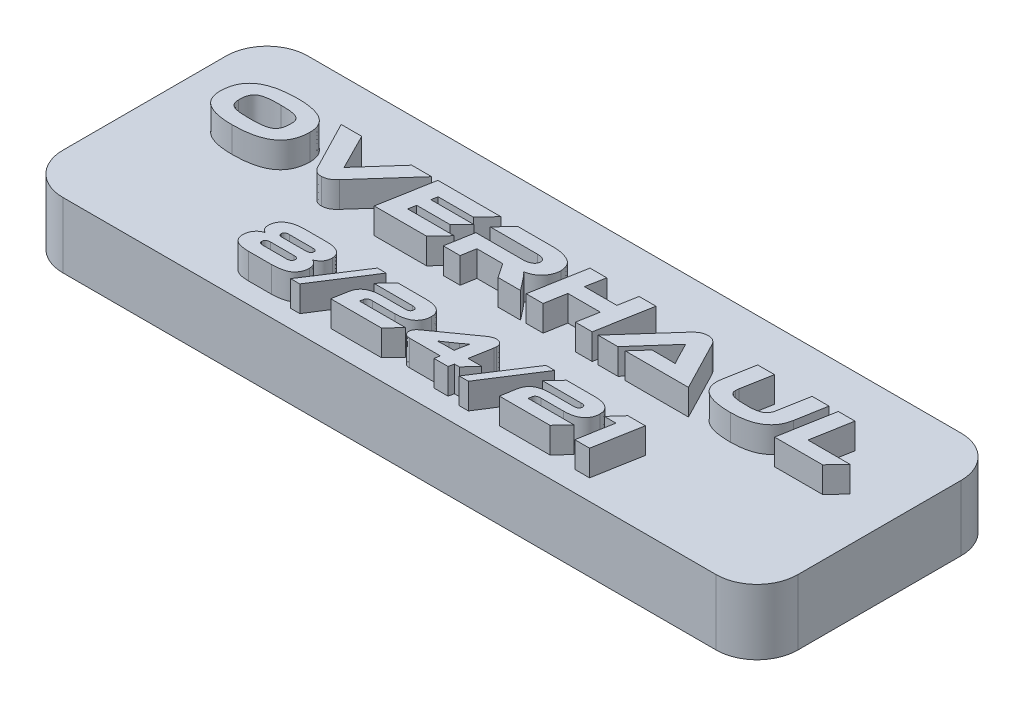
SolidWorks part; units mm, degrees
ref_plane "Front Plane" through (0, 0, 0) normal (0, 0, 1) x (1, 0, 0)
ref_plane "Top Plane" through (0, 0, 0) normal (0, 1, 0) x (1, 0, 0)
ref_plane "Right Plane" through (0, 0, 0) normal (1, 0, 0) x (0, 0, -1)
sketch "Sketch1" plane through (0, 0, 0) normal (0, 1, 0) x (1, 0, 0)
  line L1 (-28.575, 9.525) -> (28.575, 9.525)
  line L2 (-28.575, 9.525) -> (-28.575, -9.525)
  line L3 (-28.575, -9.525) -> (28.575, -9.525)
  line L4 (28.575, 9.525) -> (28.575, -9.525)
  line L5 (-28.575, 9.525) -> (28.575, -9.525) construction
  line L6 (-28.575, -9.525) -> (28.575, 9.525) construction
  point P0 (0, 0)
  dimension "D1" = 57.15
  dimension "D2" = 19.05
extrude "Boss-Extrude1" add sketch "Sketch1" along normal up to surface (5.08 mm away)
fillet "Fillet1" radius 3.175 4 edges at (-28.575, 2.54, 9.525) (-28.575, 2.54, -9.525) (28.575, 2.54, 9.525) (28.575, 2.54, -9.525)
sketch "Sketch3" plane through (0, 5.08, 0) normal (0, 1, 0) x (1, 0, 0)
  line L0 (28.575, -7.9375) -> (-28.575, -7.9375) construction
  line L1 (28.575, -6.35) -> (28.575, 6.35) construction
  line L2 (-28.575, 6.35) -> (-28.575, -6.35) construction
  line L3 (28.575, 0) -> (-28.575, 0) construction
  line L5 (-25.4, -9.525) -> (25.4, -9.525) construction
  line L6 (25.4, 9.525) -> (-25.4, 9.525) construction
  text T0 "OVERHAUL" font "Ethnocentric Rg" height in points 16
  text T1 "8/24/21" font "Ethnocentric Rg" height in points 14
  point P8 (-28.575, 0)
  dimension "D1" = 1.5875
extrude "Boss-Extrude2" add sketch "Sketch3" along normal blind 2
sketch "Sketch4" plane through (0, 0, 0) normal (0, -1, 0) x (1, 0, 0)
  line L0 (25.4, 0) -> (-25.4, 0) construction
  circle A0 centre (-25.4, 0) radius 0.9
  circle A1 centre (25.4, 0) radius 0.9
  point P3 (0, 0)
  dimension "D2" = 1.8
  dimension "D1" = 50.8
extrude "Cut-Extrude1" cut sketch "Sketch4" against normal blind 4
